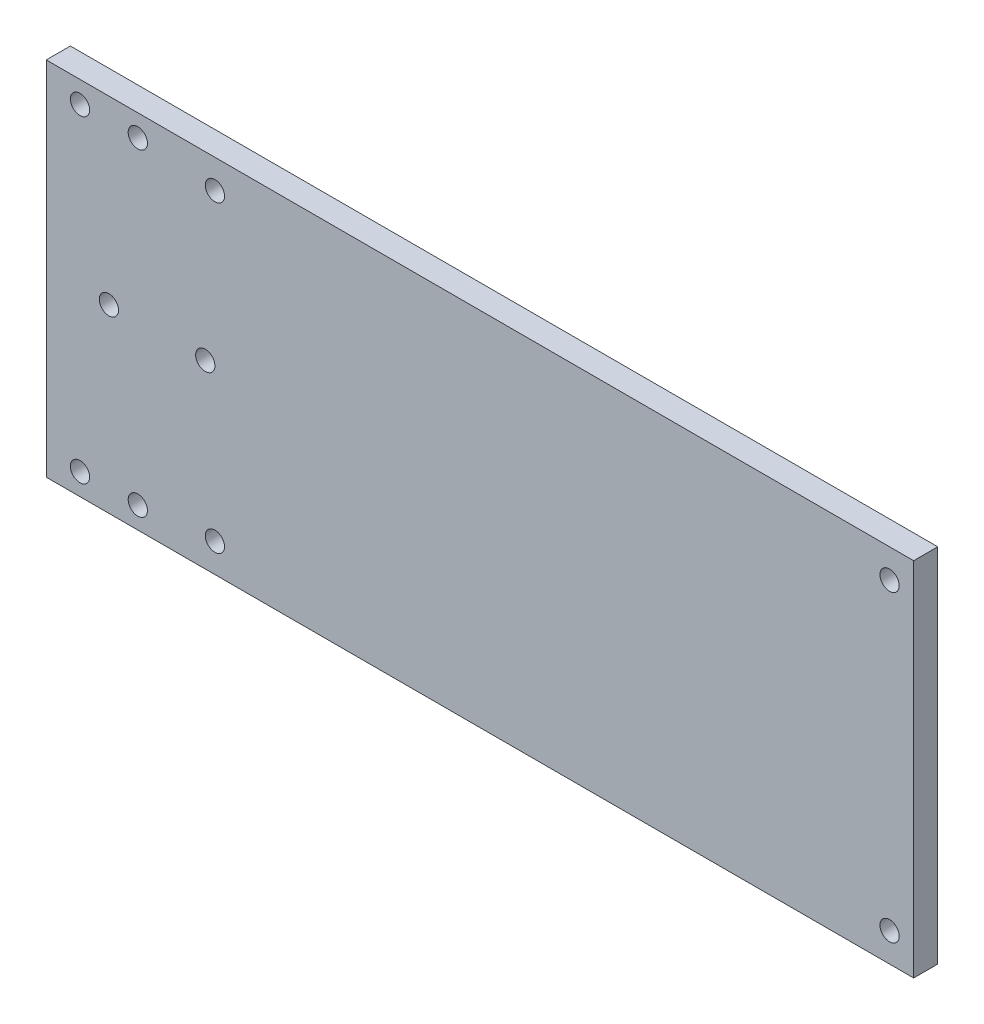
SolidWorks part; units mm, degrees
material "Acrílico (médio-alto impacto)"
ref_plane "Plano frontal" through (0, 0, 0) normal (0, 0, 1) x (1, 0, 0)
ref_plane "Plano superior" through (0, 0, 0) normal (0, 1, 0) x (1, 0, 0)
ref_plane "Plano direito" through (0, 0, 0) normal (1, 0, 0) x (0, 0, -1)
sketch "Esboço1" plane through (0, 0, 0) normal (0, 0, 1) x (1, 0, 0)
  line L0 (-71, 33) -> (-83, -33) construction
  line L1 (-90, -37.5) -> (90, -37.5)
  line L2 (-90, -37.5) -> (-90, 37.5)
  line L3 (-90, 37.5) -> (90, 37.5)
  line L4 (-87, 0) -> (-67, 0) construction
  line L5 (-90, -37.5) -> (90, 37.5) construction
  line L6 (-90, 37.5) -> (90, -37.5) construction
  line L7 (0, 0) -> (-24.7724, 0) construction
  line L8 (90, -37.5) -> (90, 37.5)
  circle A0 centre (-83, 33) radius 2
  circle A1 centre (-71, 33) radius 2
  circle A2 centre (-71, -33) radius 2
  circle A3 centre (-77, 0) radius 2
  circle A4 centre (-83, -33) radius 2
  circle A5 centre (-57, 0) radius 2
  circle A6 centre (-55, 31.5) radius 2
  circle A7 centre (85, 31.5) radius 2
  circle A8 centre (85, -31.5) radius 2
  circle A9 centre (-55, -31.5) radius 2
  point P0 (0, 0)
  point P11 (85.3, 0)
  point P20 (-90, 0)
  point P25 (-77, 0)
  point P29 (0, 0)
  dimension "D4" = 2
  dimension "D5" = 2
  dimension "D3" = 4
  dimension "D9" = 10
  dimension "D10" = 4
  dimension "D12" = 4
  dimension "D14" = 12
  dimension "D1" = 180
  dimension "D2" = 75
  dimension "D6" = 4.5
  dimension "D7" = 7
  dimension "D8" = 20
  dimension "D11" = 6
  dimension "D13" = 35
  dimension "D15" = 140
extrude "Ressalto-extrusão1" add sketch "Esboço1" along normal blind 5
